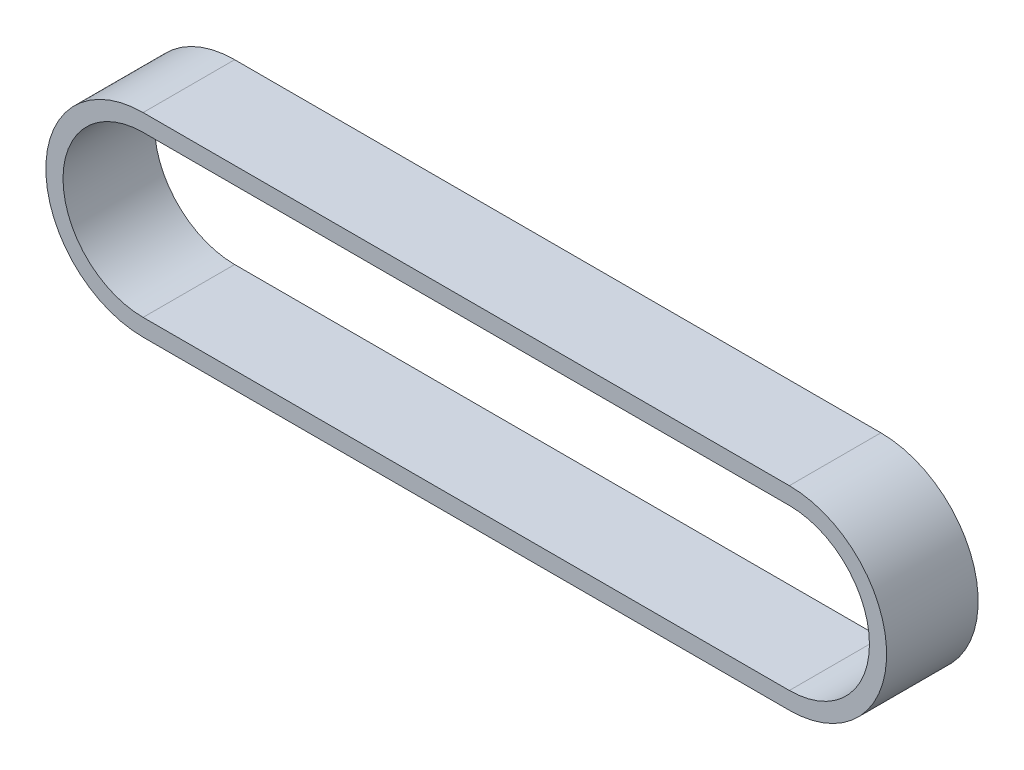
SolidWorks part; units mm, degrees
material "PF"
ref_plane "Piano frontale" through (0, 0, 0) normal (0, 0, 1) x (1, 0, 0)
ref_plane "Piano superiore" through (0, 0, 0) normal (0, 1, 0) x (1, 0, 0)
ref_plane "Piano destro" through (0, 0, 0) normal (1, 0, 0) x (0, 0, -1)
sketch "Schizzo1" plane through (0, 0, 0) normal (0, 0, 1) x (1, 0, 0)
  line L0 (0, 0) -> (-45.1774, 0) construction
  line L1 (0, -5.6) -> (-45.1774, -5.6)
  line L2 (0, 5.6) -> (-45.1774, 5.6)
  line L3 (0, 0) -> (-45.1774, 0) construction
  line L4 (0, -6.8) -> (-45.1774, -6.8)
  line L5 (0, 6.8) -> (-45.1774, 6.8)
  arc A0 (0, -5.6) -> (0, 5.6) centre (0, 0) ccw
  arc A1 (-45.1774, 5.6) -> (-45.1774, -5.6) centre (-45.1774, 0) ccw
  arc A2 (0, -6.8) -> (0, 6.8) centre (0, 0) ccw
  arc A3 (-45.1774, 6.8) -> (-45.1774, -6.8) centre (-45.1774, 0) ccw
  point P3 (-22.5887, 0)
  point P8 (-22.5887, 0)
  line B0 (0, 0) -> (-45.1774, 0) construction
  dimension "D2" = 5.6
  dimension "D1" = 1.2
sketch_block_instance "puleggia piccola-1"
sketch_block "puleggia piccola"
extrude "Estrusione-Estrusione2" add sketch "Schizzo1" along normal blind 6.4 contours L5 A3 L4 A2 A1 L2 A0 L1
